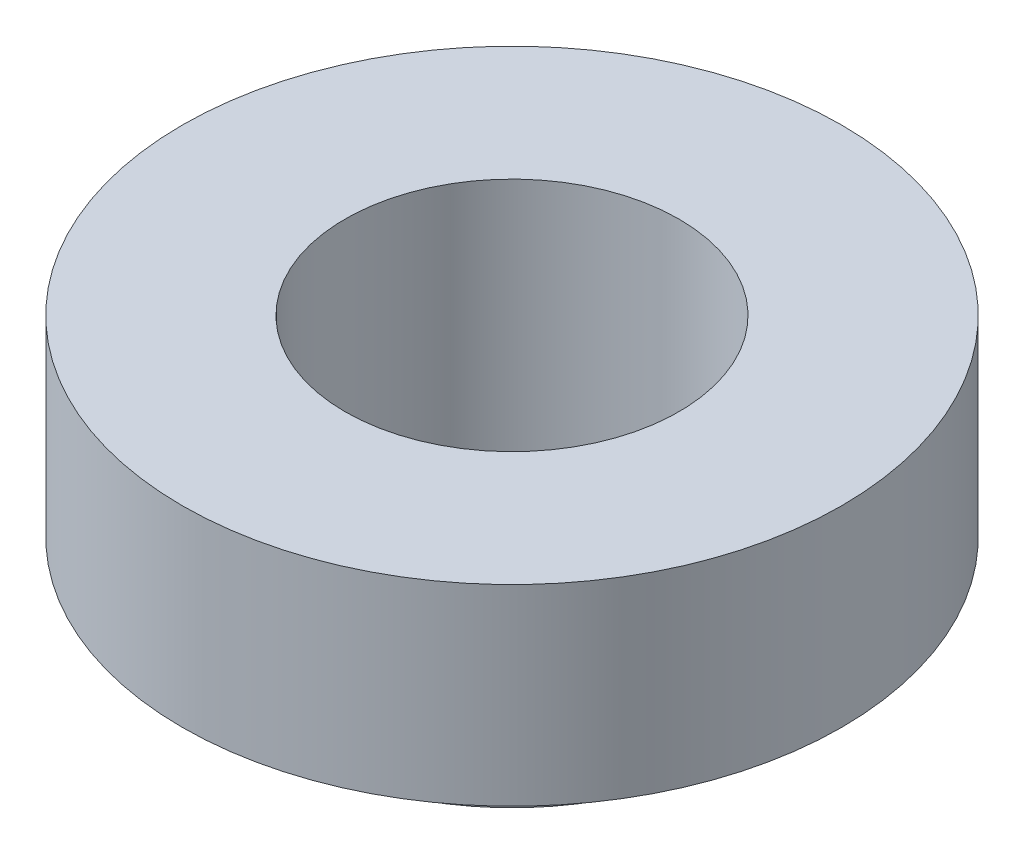
SolidWorks part; units mm, degrees
material "AISI 1015 鋼, 冷間引抜 (SS)"
ref_plane "正面" through (0, 0, 0) normal (0, 0, 1) x (1, 0, 0)
ref_plane "平面" through (0, 0, 0) normal (0, 1, 0) x (1, 0, 0)
ref_plane "右側面" through (0, 0, 0) normal (1, 0, 0) x (0, 0, -1)
sketch "ｽｹｯﾁ1" plane through (0, 0, 0) normal (0, 1, 0) x (1, 0, 0)
  circle A0 centre (0, 0) radius 3.95
  dimension "D1" = 7.9
extrude "ﾎﾞｽ - 押し出し1" add sketch "ｽｹｯﾁ1" along normal blind 2.3
sketch "ｽｹｯﾁ3" plane through (0, 0, 0) normal (0, -1, 0) x (-1, 0, 0)
  circle A0 centre (0, 0) radius 2.7
  dimension "D1" = 5.4
extrude "ﾎﾞｽ - 押し出し2" add sketch "ｽｹｯﾁ3" along normal blind 0.9
sketch "ｽｹｯﾁ4" plane through (0, -0.9, 0) normal (0, -1, 0) x (-1, 0, 0)
  circle A0 centre (0, 0) radius 2
  dimension "D1" = 4
extrude "ｶｯﾄ - 押し出し1" cut sketch "ｽｹｯﾁ4" against normal blind 3.3
